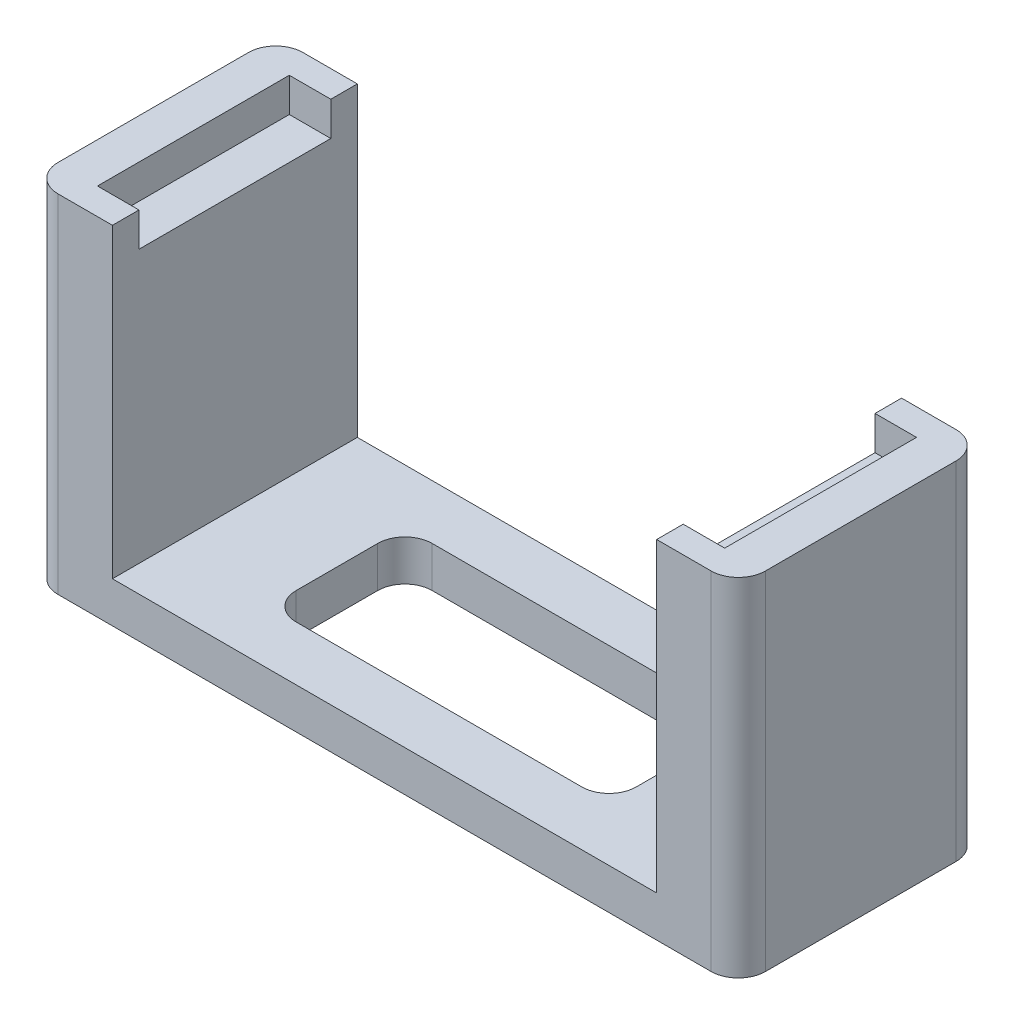
SolidWorks part; units mm, degrees
ref_plane "Front Plane" through (0, 0, 0) normal (0, 0, 1) x (1, 0, 0)
ref_plane "Top Plane" through (0, 0, 0) normal (0, 1, 0) x (1, 0, 0)
ref_plane "Right Plane" through (0, 0, 0) normal (1, 0, 0) x (0, 0, -1)
sketch "Sketch1" plane through (0, 0, 0) normal (0, 1, 0) x (1, 0, 0)
  line L1 (-26, 9) -> (26, 9)
  line L2 (-26, 9) -> (-26, -9)
  line L3 (-26, -9) -> (26, -9)
  line L4 (26, 9) -> (26, -9)
  line L5 (0, -9) -> (0, 9) construction
  line L6 (-26, 0) -> (26, 0) construction
  point P264 (0, 0)
  dimension "D1" = 52
  dimension "D2" = 18
extrude "Boss-Extrude1" add sketch "Sketch1" along normal blind 25.5
sketch "Sketch2" plane through (0, 25.5, 0) normal (0, 1, 0) x (1, 0, 0)
  line L0 (-13.75, 0) -> (13.75, 0) construction
  line L1 (-23.05, 7.05) -> (23.05, 7.05)
  line L2 (-23.05, 7.05) -> (-23.05, -7.05)
  line L3 (-23.05, -7.05) -> (23.05, -7.05)
  line L4 (23.05, 7.05) -> (23.05, -7.05)
  line L5 (0, -7.05) -> (0, 7.05) construction
  line L6 (-23.05, 0) -> (23.05, 0) construction
  line L7 (0, -9.9) -> (0, 9.9) construction
  point P244 (0, 0)
  dimension "D1" = 14.1
  dimension "D2" = 46.1
extrude "Cut-Extrude1" cut sketch "Sketch2" against normal blind 2.5
sketch "Sketch4" plane through (0, 25.5, 0) normal (0, 1, 0) x (1, 0, 0)
  line L0 (-13.75, 0) -> (13.75, 0) construction
  line L1 (-20, 9) -> (20, 9)
  line L2 (-20, 9) -> (-20, -9)
  line L3 (-20, -9) -> (20, -9)
  line L4 (20, 9) -> (20, -9)
  line L5 (0, -9) -> (0, 9) construction
  line L6 (-20, 0) -> (20, 0) construction
  line L7 (0, -9.9) -> (0, 9.9) construction
  line L8 (26, 9) -> (-26, 9) construction
  point P232 (0, 0)
  dimension "D1" = 40
extrude "Cut-Extrude2" cut sketch "Sketch4" against normal offset from surface (22.5 mm away) 3 up to face at (0, 0, 0)
sketch "Sketch5" plane through (0, 3, 0) normal (0, 1, 0) x (1, 0, 0)
  line L1 (-12.5, 5) -> (12.5, 5)
  line L2 (-12.5, 5) -> (-12.5, -5)
  line L3 (-12.5, -5) -> (12.5, -5)
  line L4 (12.5, 5) -> (12.5, -5)
  line L5 (0, -5) -> (0, 5) construction
  line L6 (-12.5, 0) -> (12.5, 0) construction
  point P408 (0, 0)
  dimension "D1" = 10
  dimension "D2" = 25
extrude "Cut-Extrude3" cut sketch "Sketch5" against normal through all
fillet "Fillet1" radius 2 4 edges at (-26, 12.75, 9) (26, 12.75, -9) (-26, 12.75, -9) (26, 12.75, 9)
fillet "Fillet2" radius 2 4 edges at (12.5, 1.5, 5) (-12.5, 1.5, 5) (-12.5, 1.5, -5) (12.5, 1.5, -5)
